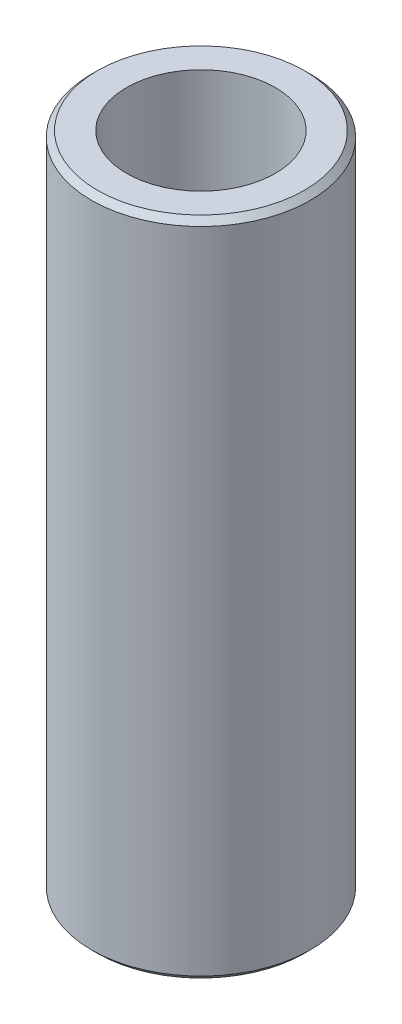
SolidWorks part; units mm, degrees
material "6061-T6 (SS)"
ref_plane "Front Plane" through (0, 0, 0) normal (0, 0, 1) x (1, 0, 0)
ref_plane "Top Plane" through (0, 0, 0) normal (0, 1, 0) x (1, 0, 0)
ref_plane "Right Plane" through (0, 0, 0) normal (1, 0, 0) x (0, 0, -1)
sketch "Sketch1" plane through (0, 0, 0) normal (0, 1, 0) x (1, 0, 0)
  circle A0 centre (0, 0) radius 4.7625
  dimension "D1" = 9.525
extrude "Boss-Extrude1" add sketch "Sketch1" along normal mid plane 28.7625
chamfer "Chamfer1" distance 0.254 angle 45 2 edges at (0, 14.3813, 4.7625) (0, -14.3813, 4.7625)
sketch "Sketch2" plane through (0, -14.3813, 0) normal (0, -1, 0) x (1, 0, 0)
  circle A0 centre (0, 0) radius 3.2385
  dimension "D1" = 6.477
extrude "Cut-Extrude1" cut sketch "Sketch2" against normal through all
equation "\"D1@Boss-Extrude1\"=28.7625mm"
